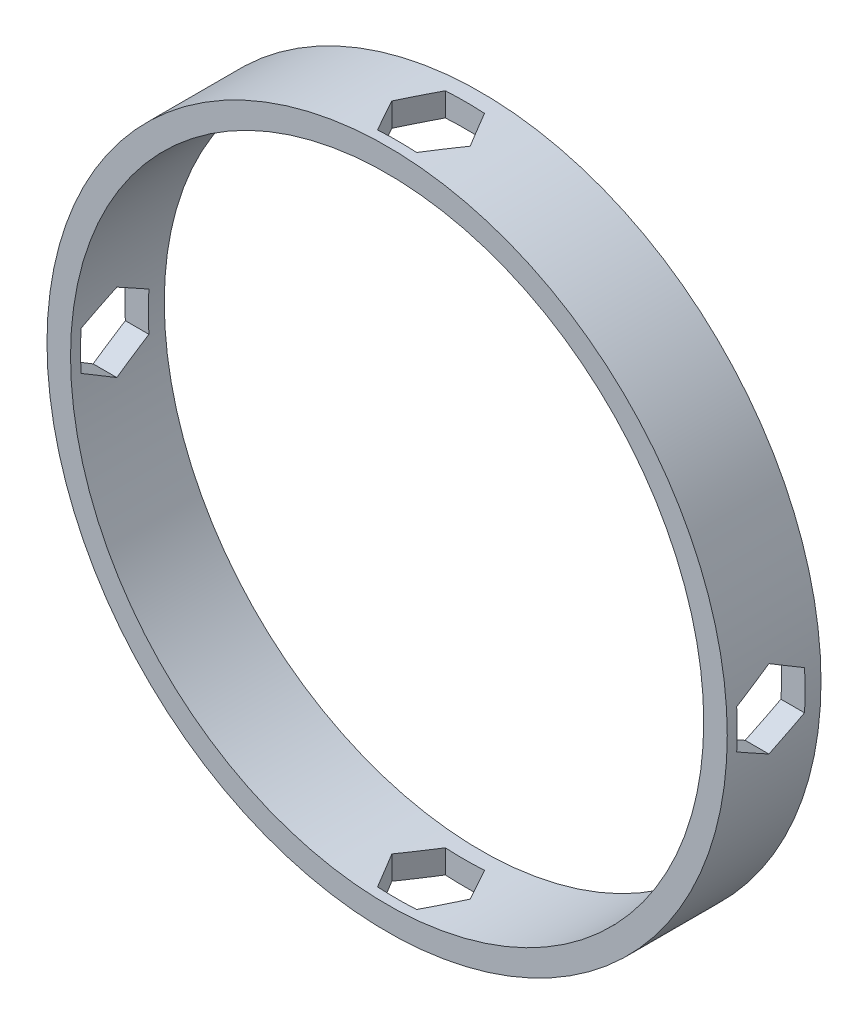
SolidWorks part; units mm, degrees
ref_plane "Front Plane" through (0, 0, 0) normal (0, 0, 1) x (1, 0, 0)
ref_plane "Top Plane" through (0, 0, 0) normal (0, 1, 0) x (1, 0, 0)
ref_plane "Right Plane" through (0, 0, 0) normal (1, 0, 0) x (0, 0, -1)
sketch "Sketch1" plane through (0, 0, 0) normal (0, 0, 1) x (1, 0, 0)
  circle A0 centre (0, 0) radius 34.11
  circle A1 centre (0, 0) radius 31.75
  dimension "D1" = 68.22
  dimension "D2" = 63.5
extrude "Boss-Extrude1" add sketch "Sketch1" along normal blind 9.4
ref_plane "Plane1" through (0, 34.11, 0) normal (0, 1, 0) x (1, 0, 0)
sketch "Sketch2" plane through (0, 34.11, 0) normal (0, 1, 0) x (1, 0, 0)
  line L0 (0, -5) -> (-3.926, -5) construction
  line L1 (3.926, -5) -> (1.963, -1.6)
  line L2 (1.963, -1.6) -> (-1.963, -1.6)
  line L3 (-1.963, -1.6) -> (-3.926, -5)
  line L4 (-3.926, -5) -> (-1.963, -8.4)
  line L5 (-1.963, -8.4) -> (1.963, -8.4)
  line L6 (1.963, -8.4) -> (3.926, -5)
  circle A1 centre (0, -5) radius 3.4 construction
  dimension "D2" = 5
  dimension "D3" = 6.8
extrude "Cut-Extrude1" cut sketch "Sketch2" against normal through all
pattern_circular "CirPattern2" count 2 every 90 about axis through (0, 0, 9.4) along (0, 0, 1) of "Cut-Extrude1"
